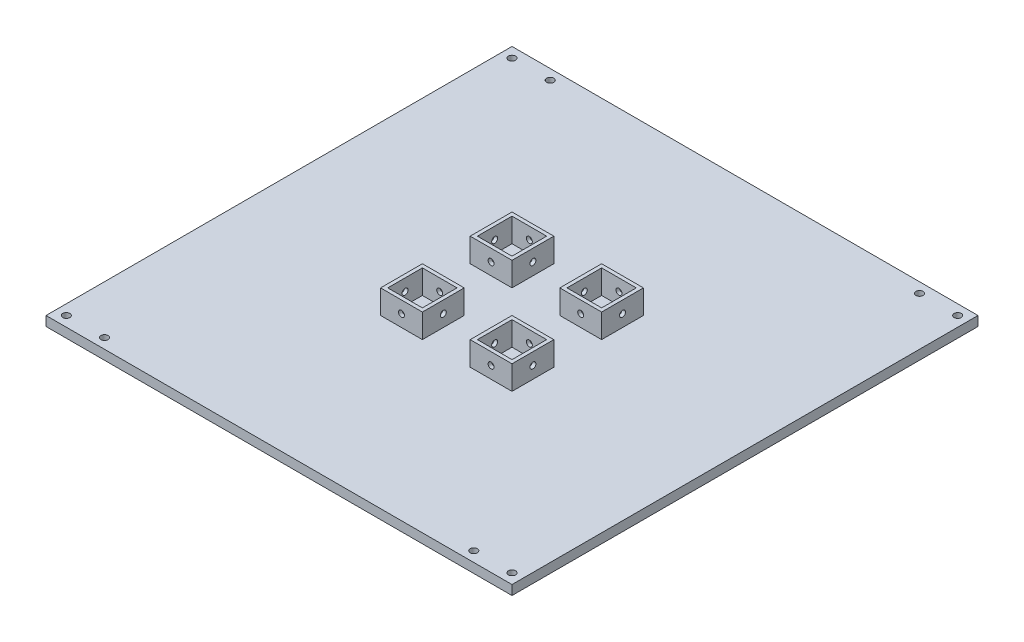
SolidWorks part; units mm, degrees
ref_plane "Front Plane" through (0, 0, 0) normal (0, 0, 1) x (1, 0, 0)
ref_plane "Top Plane" through (0, 0, 0) normal (0, 1, 0) x (1, 0, 0)
ref_plane "Right Plane" through (0, 0, 0) normal (1, 0, 0) x (0, 0, -1)
sketch "Sketch1" plane through (0, 0, 0) normal (0, 1, 0) x (1, 0, 0)
  line L1 (-97.5, -97.5) -> (97.5, -97.5)
  line L2 (-97.5, -97.5) -> (-97.5, 97.5)
  line L3 (-97.5, 97.5) -> (97.5, 97.5)
  line L4 (97.5, -97.5) -> (97.5, 97.5)
  line L5 (-97.5, -97.5) -> (97.5, 97.5) construction
  line L6 (-97.5, 97.5) -> (97.5, -97.5) construction
  point P0 (0, 0)
  dimension "D1" = 195
  dimension "D2" = 195
extrude "Boss-Extrude1" add sketch "Sketch1" along normal blind 4
sketch "Sketch2" plane through (0, 4, 0) normal (0, 1, 0) x (1, 0, 0)
  line L0 (0, 0) -> (-10, 10) construction
  line L1 (0, 0) -> (-10, 0) construction
  line L2 (-10, 0) -> (-10, 10) construction
  line L4 (-10, 10) -> (-27.5, 10)
  line L5 (-10, 10) -> (-10, 27.5)
  line L6 (-10, 27.5) -> (-27.5, 27.5)
  line L7 (-27.5, 10) -> (-27.5, 27.5)
  dimension "D1" = 45
  dimension "D2" = 17.5
  dimension "D3" = 10
extrude "Boss-Extrude2" add sketch "Sketch2" along normal blind 10
sketch "Sketch3" plane through (0, 14, 0) normal (0, 1, 0) x (1, 0, 0)
  line L8 (-11.5, 11.5) -> (-11.5, 26)
  line L9 (-11.5, 26) -> (-26, 26)
  line L10 (-26, 26) -> (-26, 11.5)
  line L11 (-26, 11.5) -> (-11.5, 11.5)
  line L12 (-11.5, 11.5) -> (-11.5, 26)
  line L13 (-11.5, 26) -> (-26, 26)
  line L14 (-26, 26) -> (-26, 11.5)
  line L15 (-26, 11.5) -> (-11.5, 11.5)
  dimension "D1" = 1.5
extrude "Cut-Extrude1" cut sketch "Sketch3" against normal up to surface (10 mm away) up to face at (0, 4, 0)
hole_wizard "Tap Drill for M3x0.5 Tap1" positions "Sketch4" profile "Sketch5" hole size "M3x0.5" standard "ANSI Metric" end condition through all
sketch "Sketch4" plane through (0, 0, -10) normal (0, 0, 1) x (1, 0, 0)
  line L0 (-27.5, 14) -> (-10, 4) construction
  point P6 (-18.75, 9)
sketch "Sketch5" plane through (-18.75, 9, -10) normal (1, 0, 0) x (0, -1, 0)
  line L0 (0, 0) -> (0, 87.5)
  line L1 (0, 87.5) -> (1.25, 87.5)
  line L2 (1.25, 87.5) -> (1.25, 0)
  line L5 (1.25, 0) -> (0, 0)
  line L11 (0, -6.35) -> (0, 107.95) construction
  dimension "Thru Hole Dia." = 2.5
  dimension "Thru Hole Depth" = 87.5
hole_wizard "Tap Drill for M3x0.5 Tap2" positions "Sketch6" profile "Sketch7" hole size "M3x0.5" standard "ANSI Metric" end condition through all
sketch "Sketch6" plane through (-27.5, 0, 0) normal (-1, 0, 0) x (0, 0, 1)
  line L0 (-27.5, 14) -> (-10, 4) construction
  point P7 (-18.75, 9)
sketch "Sketch7" plane through (-27.5, 9, -18.75) normal (0, 1, 0) x (0, 0, 1)
  line L0 (0, 0) -> (0, 125)
  line L1 (0, 125) -> (1.25, 125)
  line L2 (1.25, 125) -> (1.25, 0)
  line L5 (1.25, 0) -> (0, 0)
  line L11 (0, -6.35) -> (0, 107.95) construction
  dimension "Thru Hole Dia." = 2.5
  dimension "Thru Hole Depth" = 125
ref_plane "Plane1" through (0, 0, 0) normal (-1, 0, 0) x (0, 0, 1)
ref_plane "Plane2" through (0, 0, 0) normal (0, 0, -1) x (-1, 0, 0)
mirror "Mirror1" about plane through (0, 0, 0) normal (0, 0, -1) of "Tap Drill for M3x0.5 Tap2", "Tap Drill for M3x0.5 Tap1", "Cut-Extrude1", "Boss-Extrude2"
mirror "Mirror2" about plane through (0, 0, 0) normal (-1, 0, 0) of "Mirror1", "Boss-Extrude2", "Cut-Extrude1", "Tap Drill for M3x0.5 Tap1", "Tap Drill for M3x0.5 Tap2"
sketch "Sketch8" plane through (0, 4, 0) normal (0, 1, 0) x (1, 0, 0)
  circle A0 centre (77.25, 93.25) radius 1.5
  circle A1 centre (93.25, 93.25) radius 1.5
  dimension "D1" = 3
  dimension "D2" = 3
extrude "Cut-Extrude2" cut sketch "Sketch8" against normal up to next (4 mm away)
mirror "Mirror3" about plane through (0, 0, 0) normal (-1, 0, 0) of "Cut-Extrude2"
mirror "Mirror4" about plane through (0, 0, 0) normal (0, 0, -1) of "Mirror3", "Cut-Extrude2"
